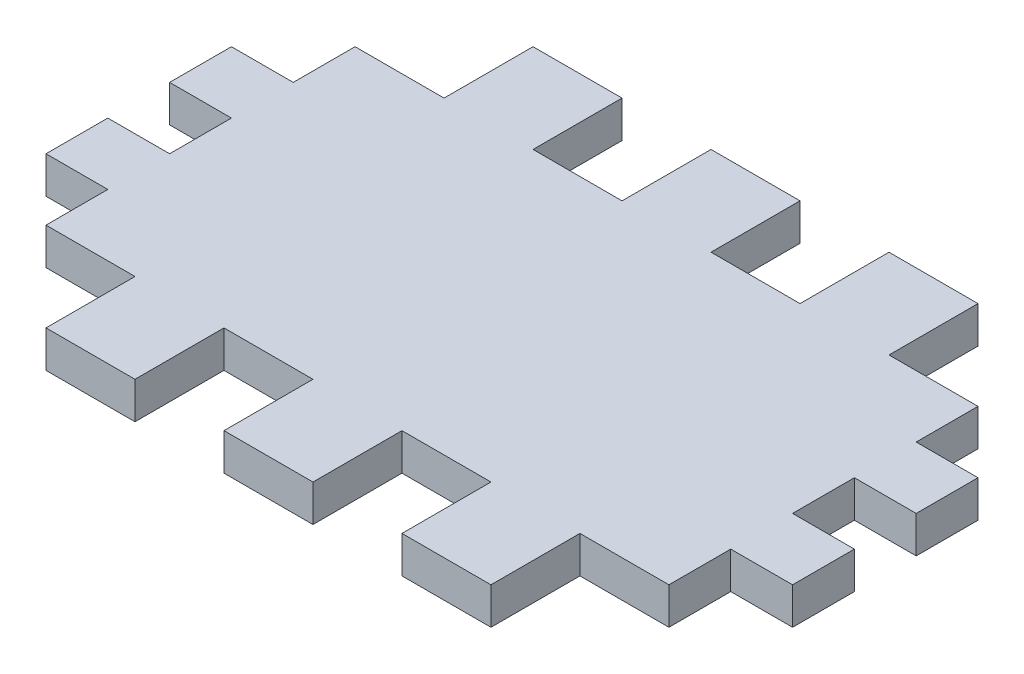
SolidWorks part; units mm, degrees
ref_plane "Front Plane" through (0, 0, 0) normal (0, 0, 1) x (1, 0, 0)
ref_plane "Top Plane" through (0, 0, 0) normal (0, 1, 0) x (1, 0, 0)
ref_plane "Right Plane" through (0, 0, 0) normal (1, 0, 0) x (0, 0, -1)
sketch "Sketch3" plane through (0, 0, 0) normal (0, 1, 0) x (1, 0, 0)
  line L0 (-273.0262, 15.44) -> (-250.7977, 15.44)
  line L1 (-250.7977, 15.44) -> (-250.7977, 37.6686)
  line L2 (-250.7977, 37.6686) -> (-228.5691, 37.6686)
  line L3 (-228.5691, 37.6686) -> (-228.5691, 15.44)
  line L4 (-228.5691, 15.44) -> (-206.3405, 15.44)
  line L5 (-206.3405, 15.44) -> (-206.3405, 37.6686)
  line L6 (-206.3405, 37.6686) -> (-184.1119, 37.6686)
  line L7 (-184.1119, 37.6686) -> (-184.1119, 15.44)
  line L8 (-184.1119, 15.44) -> (-161.8834, 15.44)
  line L9 (-161.8834, 15.44) -> (-161.8834, 37.6686)
  line L10 (-161.8834, 37.6686) -> (-139.6548, 37.6686)
  line L11 (-139.6548, 37.6686) -> (-139.6548, 15.44)
  line L12 (-139.6548, 15.44) -> (-117.4262, 15.44)
  line L13 (-117.4262, 15.44) -> (-117.4262, 0)
  line L14 (-117.4262, 0) -> (-101.9862, 0)
  line L15 (-101.9862, 0) -> (-101.9862, -15.44)
  line L16 (-101.9862, -15.44) -> (-117.4262, -15.44)
  line L17 (-117.4262, -15.44) -> (-117.4262, -30.88)
  line L18 (-117.4262, -30.88) -> (-101.9862, -30.88)
  line L19 (-101.9862, -30.88) -> (-101.9862, -46.32)
  line L20 (-101.9862, -46.32) -> (-117.4262, -46.32)
  line L21 (-117.4262, -46.32) -> (-117.4262, -61.76)
  line L22 (-117.4262, -61.76) -> (-139.6548, -61.76)
  line L23 (-139.6548, -61.76) -> (-139.6548, -83.9886)
  line L24 (-139.6548, -83.9886) -> (-161.8834, -83.9886)
  line L25 (-161.8834, -83.9886) -> (-161.8834, -61.76)
  line L26 (-161.8834, -61.76) -> (-184.1119, -61.76)
  line L27 (-184.1119, -61.76) -> (-184.1119, -83.9886)
  line L28 (-184.1119, -83.9886) -> (-206.3405, -83.9886)
  line L29 (-206.3405, -83.9886) -> (-206.3405, -61.76)
  line L30 (-206.3405, -61.76) -> (-228.5691, -61.76)
  line L31 (-228.5691, -61.76) -> (-228.5691, -83.9886)
  line L32 (-228.5691, -83.9886) -> (-250.7977, -83.9886)
  line L33 (-250.7977, -83.9886) -> (-250.7977, -61.76)
  line L34 (-250.7977, -61.76) -> (-273.0262, -61.76)
  line L35 (-273.0262, -61.76) -> (-273.0262, -46.32)
  line L36 (-273.0262, -46.32) -> (-288.4662, -46.32)
  line L37 (-288.4662, -46.32) -> (-288.4662, -30.88)
  line L38 (-288.4662, -30.88) -> (-273.0262, -30.88)
  line L39 (-273.0262, -30.88) -> (-273.0262, -15.44)
  line L40 (-273.0262, -15.44) -> (-288.4662, -15.44)
  line L41 (-288.4662, -15.44) -> (-288.4662, 0)
  line L42 (-288.4662, 0) -> (-273.0262, 0)
  line L43 (-273.0262, 0) -> (-273.0262, 15.44)
  dimension "D1" = 22.2286
  dimension "D2" = 22.2286
  dimension "D3" = 22.2286
  dimension "D4" = 22.2286
  dimension "D5" = 22.2286
  dimension "D6" = 22.2286
  dimension "D7" = 22.2286
  dimension "D8" = 22.2286
  dimension "D9" = 22.2286
  dimension "D10" = 22.2286
  dimension "D11" = 22.2286
  dimension "D12" = 22.2286
  dimension "D13" = 22.2286
  dimension "D14" = 22.2286
  dimension "D15" = 22.2286
  dimension "D16" = 22.2286
  dimension "D17" = 22.2286
  dimension "D18" = 22.2286
  dimension "D19" = 22.2286
  dimension "D20" = 22.2286
  dimension "D21" = 22.2286
  dimension "D22" = 22.2286
  dimension "D23" = 22.2286
  dimension "D24" = 22.2286
  dimension "D25" = 22.2286
  dimension "D26" = 22.2286
  dimension "D27" = 15.44
  dimension "D28" = 15.44
  dimension "D29" = 15.44
  dimension "D30" = 15.44
  dimension "D31" = 15.44
  dimension "D32" = 15.44
  dimension "D33" = 15.44
  dimension "D34" = 15.44
  dimension "D35" = 15.44
  dimension "D36" = 15.44
  dimension "D37" = 15.44
  dimension "D38" = 15.44
  dimension "D39" = 15.44
  dimension "D40" = 15.44
  dimension "D41" = 15.44
  dimension "D42" = 15.44
  dimension "D43" = 15.44
extrude "Boss-Extrude1" add sketch "Sketch3" along normal blind 9.2 contours L0 L1 L2 L3 L4 L5 L6 L7 L8 L9 L10 L11 L12 L13 L14 L15 L16 L17 L18 L19 L20 L21 L22 L23 L24 L25 L26 L27 L28 L29 L30 L31 L32 L33 L34 L35 L36 L37 L38 L39 L40 L41 L42 L43
